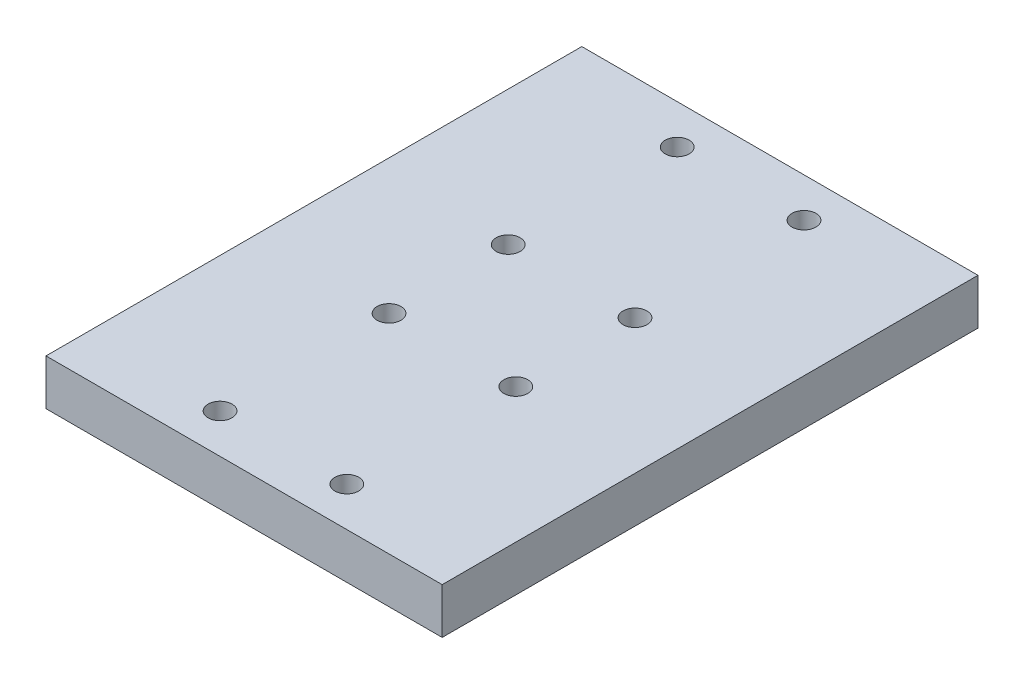
SolidWorks part; units mm, degrees
ref_plane "Front Plane" through (0, 0, 0) normal (0, 0, 1) x (1, 0, 0)
ref_plane "Top Plane" through (0, 0, 0) normal (0, 1, 0) x (1, 0, 0)
ref_plane "Right Plane" through (0, 0, 0) normal (1, 0, 0) x (0, 0, -1)
sketch "Sketch1" plane through (0, 0, 0) normal (0, 1, 0) x (1, 0, 0)
  line L0 (27.5, 74.38) -> (27.5, 0) construction
  line L1 (0, 0) -> (55, 0)
  line L2 (0, 0) -> (0, 74.38)
  line L3 (0, 74.38) -> (55, 74.38)
  line L4 (55, 0) -> (55, 74.38)
  line L5 (0, 37.19) -> (55, 37.19) construction
  circle A0 centre (18.7, 68.92) radius 1.66
  circle A1 centre (36.3, 68.92) radius 1.66
  circle A2 centre (36.3, 45.46) radius 1.66
  circle A3 centre (18.7, 45.46) radius 1.66
  circle A4 centre (18.7, 28.92) radius 1.66
  circle A5 centre (36.3, 28.92) radius 1.66
  circle A6 centre (36.3, 5.46) radius 1.66
  circle A7 centre (18.7, 5.46) radius 1.66
  point P15 (15.77, 70.4675)
  dimension "D4" = 3.32
  dimension "D1" = 74.38
  dimension "D2" = 55
  dimension "D3" = 23.46
  dimension "D5" = 17.6
  dimension "D6" = 5.46
extrude "Boss-Extrude1" add sketch "Sketch1" along normal blind 6.35
